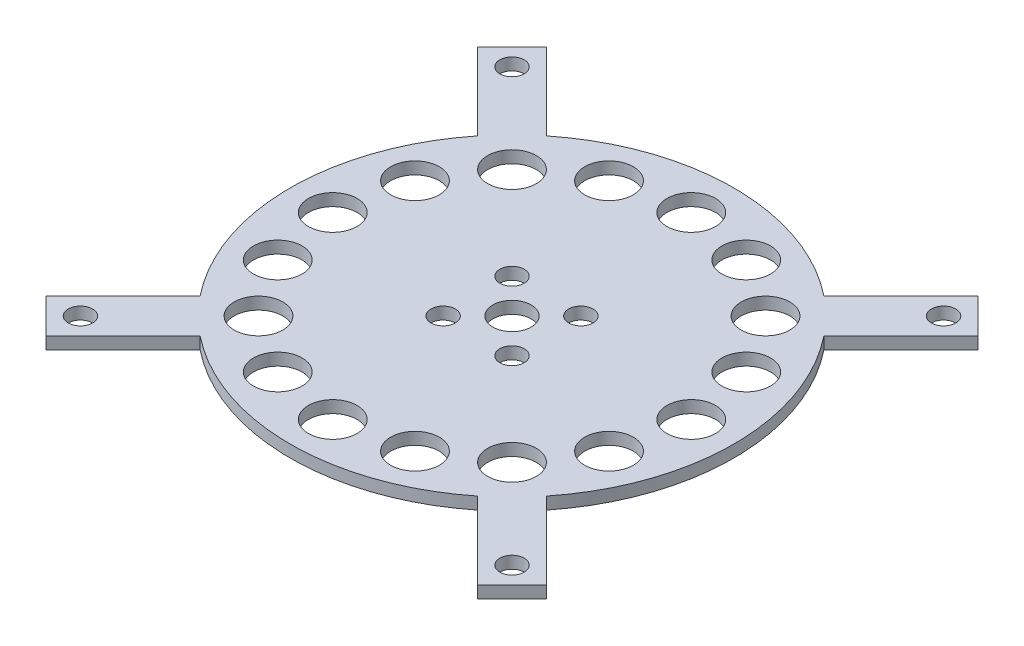
SolidWorks part; units mm, degrees
material "Nickel"
ref_plane "Front Plane" through (0, 0, 0) normal (0, 0, 1) x (1, 0, 0)
ref_plane "Top Plane" through (0, 0, 0) normal (0, 1, 0) x (1, 0, 0)
ref_plane "Right Plane" through (0, 0, 0) normal (1, 0, 0) x (0, 0, -1)
sketch "Sketch1" plane through (0, 0, 0) normal (0, 1, 0) x (1, 0, 0)
  line L0 (36.1858, 45.1661) -> (56.2882, 65.2685)
  line L1 (56.2882, 65.2685) -> (65.2685, 56.2882)
  line L2 (65.2685, 56.2882) -> (45.1661, 36.1858)
  line L3 (40.923, 40.923) -> (60.7784, 60.7784) construction
  line L4 (0, 0) -> (0, 57.8739) construction
  line L5 (45.1661, -36.1858) -> (65.2685, -56.2882)
  line L6 (40.923, -40.923) -> (60.7784, -60.7784) construction
  line L7 (56.2882, -65.2685) -> (36.1858, -45.1661)
  line L8 (65.2685, -56.2882) -> (56.2882, -65.2685)
  line L9 (-36.1858, -45.1661) -> (-56.2882, -65.2685)
  line L10 (-40.923, -40.923) -> (-60.7784, -60.7784) construction
  line L11 (-65.2685, -56.2882) -> (-45.1661, -36.1858)
  line L12 (-56.2882, -65.2685) -> (-65.2685, -56.2882)
  line L13 (-45.1661, 36.1858) -> (-65.2685, 56.2882)
  line L14 (-40.923, 40.923) -> (-60.7784, 60.7784) construction
  line L15 (-56.2882, 65.2685) -> (-36.1858, 45.1661)
  line L16 (-65.2685, 56.2882) -> (-56.2882, 65.2685)
  line L18 (-76.2, 76.2) -> (76.2, 76.2) construction
  line L19 (-76.2, 76.2) -> (-76.2, -76.2) construction
  line L20 (-76.2, -76.2) -> (76.2, -76.2) construction
  line L21 (76.2, 76.2) -> (76.2, -76.2) construction
  circle A0 centre (0, 0) radius 57.8739
  circle A1 centre (0, 0) radius 5
  point P10 (60.7784, 60.7784)
  point P32 (0, 0)
  point P34 (0, 0)
  point P36 (0, 76.2)
  point P37 (-76.2, 0)
  dimension "D2" = 10
  dimension "D1" = 115.7478
  dimension "D5" = 12.7
  dimension "D3" = 45
  dimension "D7" = 152.4
  dimension "D4" = 85.9536
  dimension "D6" = 4
extrude "Boss-Extrude1" add sketch "Sketch1" along normal blind 3.175
hole_wizard "#6 Clearance Hole1" [suppressed] positions "3DSketch2" profile "Sketch3" hole size "#6" standard "ANSI Inch"
sketch3d "3DSketch2"
  line L0 (0, 0, 0) -> (0, 0, -15.875) construction
  point P0 (0, 0, -15.875)
  dimension "D1" = 15.875
sketch "Sketch3" plane through (0, 0, -15.875) normal (1, 0, 0) x (0, 0, -1)
  line L0 (0, 0) -> (0, 13.7989)
  line L1 (0, 13.7989) -> (1.8288, 12.7)
  line L2 (1.8288, 12.7) -> (1.8288, 0)
  line L5 (1.8288, 0) -> (0, 0)
  line L10 (0, 13.7989) -> (-1.8288, 12.7) construction
  line L11 (0, -6.35) -> (0, 107.95) construction
  dimension "Hole Dia." = 3.6576
  dimension "Hole Depth" = 12.7
  dimension "Drill Angle" = 118
pattern_circular "CirPattern2" [suppressed] count 8 over 360
sketch "Sketch4" plane through (0, 3.175, 0) normal (0, 1, 0) x (1, 0, 0)
  line L0 (0, 0) -> (46.7614, 0) construction
  line L1 (46.7614, 0) -> (59.4614, 0) construction
  circle A0 centre (46.7614, 0) radius 6.35
  dimension "D1" = 12.7
  dimension "D2" = 59.4614
  dimension "D3" = 12.7
extrude "Big Inco Pin Hole" cut sketch "Sketch4" against normal through all
pattern_circular "CirPattern3" count 16 over 360 about axis through (0, 0, 0) along (0, 1, 0) of "Big Inco Pin Hole"
sketch "Sketch5" plane through (0, 3.175, 0) normal (0, 1, 0) x (1, 0, 0)
  line L0 (0, 0) -> (8.9803, 8.9803) construction
  line L1 (0, 0) -> (57.8739, 0) construction
  line L2 (8.9803, 8.9803) -> (56.2882, 56.2882) construction
  circle A0 centre (8.9803, 8.9803) radius 3.175
  arc A1 (45.1661, -36.1858) -> (45.1661, 36.1858) centre (0, 0) ccw construction
  circle A2 centre (56.2882, 56.2882) radius 3.175
  dimension "D3" = 12.7
  dimension "D2" = 6.35
  dimension "D1" = 45
  dimension "D4" = 79.6036
extrude "Small Inco Pin Hole" cut sketch "Sketch5" against normal through all
pattern_circular "CirPattern4" count 4 over 360 about axis through (0, 0, 0) along (0, 1, 0) of "Small Inco Pin Hole"
equation "\"D1@Sketch1\"=2*(\"rotor base@[TP] [Turb] Turbine.Assembly\"-1/16)"
equation "\"D2@Sketch4\"=\"rotor base@[TP] [Turb] Turbine.Assembly\""
equation "\"D4@Sketch1\"=\"rotor tip@[TP] [Turb] Turbine.Assembly\""
equation "\"D4@Sketch5\"=\"rotor tip@[TP] [Turb] Turbine.Assembly\"-1/4"
